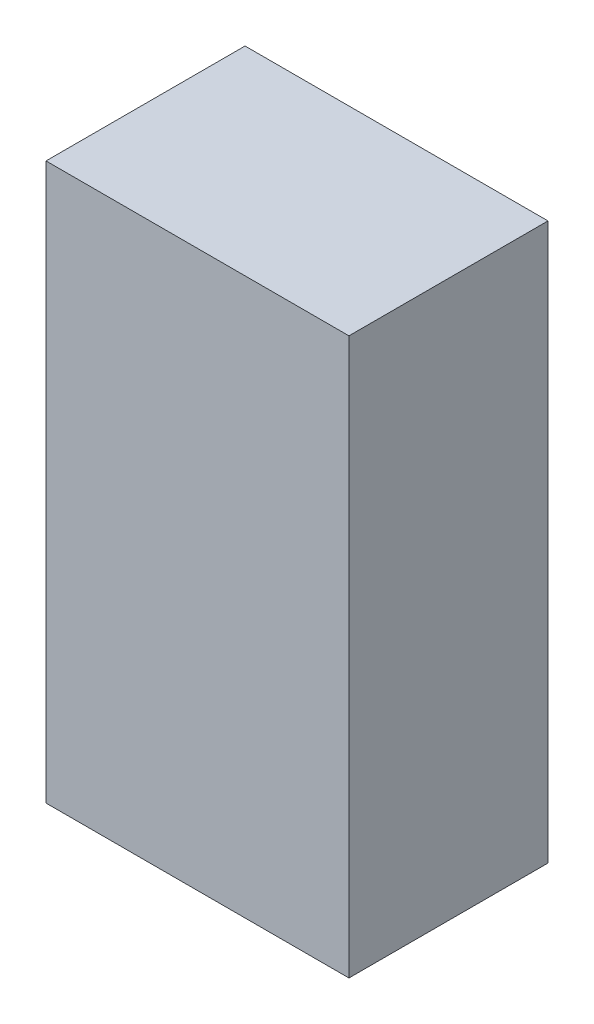
SolidWorks part; units mm, degrees
material "Plástico personalizado"
ref_plane "Plano frontal" through (0, 0, 0) normal (0, 0, 1) x (1, 0, 0)
ref_plane "Plano superior" through (0, 0, 0) normal (0, 1, 0) x (1, 0, 0)
ref_plane "Plano direito" through (0, 0, 0) normal (1, 0, 0) x (0, 0, -1)
sketch "Esboço1" plane through (0, 0, 0) normal (0, 0, 1) x (1, 0, 0)
  line L1 (0, 0) -> (20.7, 0)
  line L2 (0, 0) -> (0, -38)
  line L3 (0, -38) -> (20.7, -38)
  line L4 (20.7, 0) -> (20.7, -38)
  dimension "D1" = 38
  dimension "D2" = 20.7
extrude "Ressalto-extrusão1" add sketch "Esboço1" along normal blind 13.6
